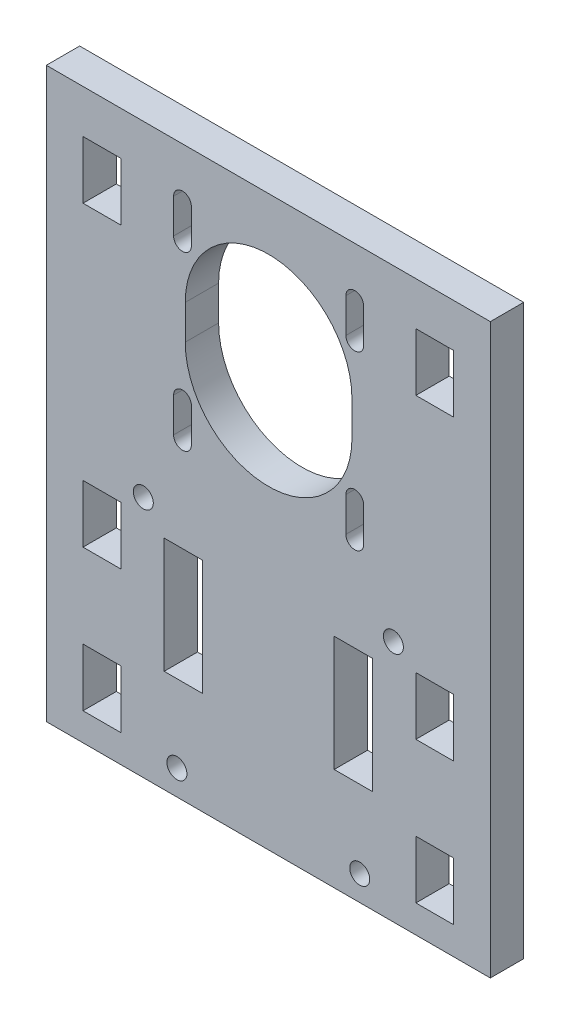
SolidWorks part; units mm, degrees
ref_plane "Plano frontal" through (0, 0, 0) normal (0, 0, 1) x (1, 0, 0)
ref_plane "Plano superior" through (0, 0, 0) normal (0, 1, 0) x (1, 0, 0)
ref_plane "Plano direito" through (0, 0, 0) normal (1, 0, 0) x (0, 0, -1)
sketch "Model" plane through (0, 0, 0) normal (0, 0, 1) x (1, 0, 0)
  line L0 (102.4373, 102.7276) -> (95.6373, 102.7276)
  line L1 (95.6373, 102.7276) -> (95.6373, 92.3276)
  line L2 (35.7373, 92.3276) -> (42.5373, 92.3276)
  line L3 (42.5373, 92.3276) -> (42.5373, 102.7276)
  line L4 (42.5373, 102.7276) -> (35.7373, 102.7276)
  line L5 (109.0373, 8.2294) -> (109.0373, 110.5276)
  line L6 (29.1373, 110.5276) -> (29.1373, 8.2294)
  line L7 (95.6373, 49.1276) -> (95.6373, 38.7276)
  line L8 (95.6373, 38.7276) -> (102.4373, 38.7276)
  line L9 (35.7373, 23.6276) -> (42.5373, 23.6276)
  line L10 (95.6373, 92.3276) -> (102.4373, 92.3276)
  line L11 (102.4373, 92.3276) -> (102.4373, 102.7276)
  line L12 (29.1373, 8.2294) -> (109.0373, 8.2294)
  line L13 (109.0373, 110.5276) -> (29.1373, 110.5276)
  line L14 (35.7373, 23.6276) -> (35.7373, 13.2276)
  line L15 (35.7373, 13.2276) -> (42.5373, 13.2276)
  line L16 (42.5373, 13.2276) -> (42.5373, 23.6276)
  line L17 (50.3373, 26.6766) -> (50.3373, 47.4451)
  line L18 (50.3373, 26.6766) -> (57.2373, 26.6766)
  line L19 (57.2373, 26.6766) -> (57.2373, 47.4451)
  line L20 (52.0373, 70.5714) -> (52.0373, 64.3714)
  line L21 (57.2373, 47.4451) -> (50.3373, 47.4451)
  line L22 (80.9373, 26.6766) -> (80.9373, 47.4451)
  line L23 (80.9373, 26.6766) -> (87.8373, 26.6766)
  line L24 (95.6373, 23.6276) -> (102.4373, 23.6276)
  line L25 (95.6373, 23.6276) -> (95.6373, 13.2276)
  line L26 (86.2373, 70.5714) -> (86.2373, 64.3714)
  line L27 (86.2373, 101.5714) -> (86.2373, 95.3714)
  line L28 (87.8373, 26.6766) -> (87.8373, 47.4451)
  line L29 (87.8373, 47.4451) -> (80.9373, 47.4451)
  line L30 (42.5373, 38.7276) -> (42.5373, 49.1276)
  line L31 (42.5373, 49.1276) -> (35.7373, 49.1276)
  line L32 (35.7373, 38.7276) -> (42.5373, 38.7276)
  line L33 (102.4373, 38.7276) -> (102.4373, 49.1276)
  line L34 (102.4373, 49.1276) -> (95.6373, 49.1276)
  line L35 (35.7373, 49.1276) -> (35.7373, 38.7276)
  line L36 (52.0373, 101.5714) -> (52.0373, 95.3714)
  line L37 (35.7373, 102.7276) -> (35.7373, 92.3276)
  line L38 (102.4373, 13.2276) -> (102.4373, 23.6276)
  line L39 (95.6373, 13.2276) -> (102.4373, 13.2276)
  line L40 (54.1373, 86.0714) -> (54.1373, 79.8714)
  line L41 (84.1373, 86.0714) -> (84.1373, 79.8714)
  line L42 (55.2373, 101.5714) -> (55.2373, 95.3714)
  line L43 (83.0373, 101.5714) -> (83.0373, 95.3714)
  line L44 (55.2373, 64.3714) -> (55.2373, 70.5714)
  line L45 (83.0373, 64.3714) -> (83.0373, 70.5714)
  circle A0 centre (52.6373, 12.7451) radius 1.8
  circle A1 centre (85.5373, 12.7451) radius 1.8
  circle A2 centre (91.5873, 51.9276) radius 1.8
  circle A3 centre (46.5873, 51.9276) radius 1.8
  arc A4 (55.2373, 101.5714) -> (52.0373, 101.5714) centre (53.6373, 101.5714) ccw
  arc A5 (52.0373, 95.3714) -> (55.2373, 95.3714) centre (53.6373, 95.3714) ccw
  arc A6 (86.2373, 101.5714) -> (83.0373, 101.5714) centre (84.6373, 101.5714) ccw
  arc A7 (83.0373, 95.3714) -> (86.2373, 95.3714) centre (84.6373, 95.3714) ccw
  arc A8 (86.2373, 70.5714) -> (83.0373, 70.5714) centre (84.6373, 70.5714) ccw
  arc A9 (83.0373, 64.3714) -> (86.2373, 64.3714) centre (84.6373, 64.3714) ccw
  arc A10 (52.0373, 64.3714) -> (55.2373, 64.3714) centre (53.6373, 64.3714) ccw
  arc A11 (55.2373, 70.5714) -> (52.0373, 70.5714) centre (53.6373, 70.5714) ccw
  arc A12 (54.1373, 79.8714) -> (84.1373, 79.8714) centre (69.1373, 79.8714) ccw
  arc A13 (84.1373, 86.0714) -> (54.1373, 86.0714) centre (69.1373, 86.0714) ccw
extrude "Ressalto-extrusão1" add sketch "Model" along normal blind 6
ref_plane "Plano1" through (39.1373, 0, 0) normal (1, 0, 0) x (0, 0, -1)
ref_plane "Plano2" through (99.0373, 0, 0) normal (-1, 0, 0) x (0, 0, 1)
ref_plane "Plano3" through (84.3873, 0, 0) normal (1, 0, 0) x (0, 0, -1)
ref_plane "Plano4" through (53.7873, 0, 0) normal (1, 0, 0) x (0, 0, -1)
ref_plane "Plano6" through (0, 37.0609, 0) normal (0, 1, 0) x (1, 0, 0)
ref_plane "Plano8" through (69.0873, 0, 0) normal (1, 0, 0) x (0, 0, -1)
ref_plane "Plano9" through (0, 57.9776, 0) normal (0, 1, 0) x (1, 0, 0)
ref_plane "Plano10" through (0, 86.0714, 0) normal (0, -1, 0) x (-1, 0, 0)
ref_plane "Plano11" through (0, 79.8714, 0) normal (0, -1, 0) x (-1, 0, 0)
ref_plane "Plano12" through (0, 82.9714, 0) normal (0, -1, 0) x (-1, 0, 0)
